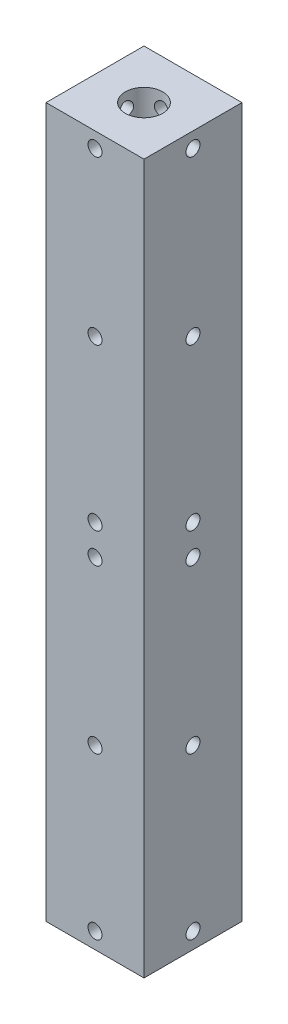
SolidWorks part; units mm, degrees
ref_plane "Front Plane" through (0, 0, 0) normal (0, 0, 1) x (1, 0, 0)
ref_plane "Top Plane" through (0, 0, 0) normal (0, 1, 0) x (1, 0, 0)
ref_plane "Right Plane" through (0, 0, 0) normal (1, 0, 0) x (0, 0, -1)
sketch "Sketch1" plane through (0, 0, 0) normal (0, 1, 0) x (1, 0, 0)
  line L1 (0, 0) -> (21, 0)
  line L2 (0, 0) -> (0, 21)
  line L3 (0, 21) -> (21, 21)
  line L4 (21, 0) -> (21, 21)
  line L5 (0, 0) -> (21, 21) construction
  line L6 (0, 21) -> (21, 0) construction
  point P4 (10.5, 10.5)
  dimension "D1" = 21
  dimension "D2" = 21
extrude "Boss-Extrude1" add sketch "Sketch1" along normal blind 152
sketch "Sketch2" plane through (0, 152, 0) normal (0, 1, 0) x (1, 0, 0)
  line L0 (0, 0) -> (21, 0) construction
  line L1 (0, 21) -> (0, 0) construction
  circle A0 centre (10.5, 10.5) radius 4
  dimension "D1" = 8
  dimension "D2" = 10.5
  dimension "D3" = 10.5
extrude "Cut-Extrude1" cut sketch "Sketch2" against normal blind 152
hole_wizard "Ø3.0mm Dowel Hole1" positions "Sketch3" profile "Sketch5" hole size "Ø3.0" standard "ANSI Metric"
sketch "Sketch3" plane through (0, 0, 0) normal (0, 0, 1) x (1, 0, 0)
  line L0 (0, 0) -> (21, 0) construction
  line L1 (0, 152) -> (0, 0) construction
  point P0 (10.5, 37.95)
  dimension "D1" = 37.95
  dimension "D2" = 10.5
sketch "Sketch5" plane through (10.5, 37.95, 0) normal (1, 0, 0) x (0, -1, 0)
  line L0 (0, 0) -> (0, 4.9013)
  line L1 (0, 4.9013) -> (1.5, 4)
  line L2 (1.5, 4) -> (1.5, 0)
  line L5 (1.5, 0) -> (0, 0)
  line L10 (0, 4.9013) -> (-1.5, 4) construction
  line L11 (0, -6.35) -> (0, 107.95) construction
  dimension "Hole Dia." = 3
  dimension "Hole Depth" = 4
  dimension "Drill Angle" = 118
pattern_linear "LPattern1" count 2 spacing 75.9 along (0, 1, 0) of "Ø3.0mm Dowel Hole1"
pattern_circular "CirPattern1" count 4 over 360 about axis through (10.5, 0, -10.5) along (0, 1, 0) of "LPattern1", "Ø3.0mm Dowel Hole1"
sketch "Sketch6" plane through (0, 0, 0) normal (0, 0, 1) x (1, 0, 0)
  line L0 (0, 152) -> (21, 152) construction
  line L1 (21, 152) -> (21, 0) construction
  circle A0 centre (10.5, 148.75) radius 1.5
  circle A1 centre (10.5, 79.35) radius 1.5
  dimension "D1" = 3
  dimension "D2" = 3.25
  dimension "D3" = 10.5
  dimension "D4" = 3
  dimension "D5" = 72.65
  dimension "D6" = 10.5
extrude "Cut-Extrude2" cut sketch "Sketch6" against normal up to next
pattern_linear "LPattern2" count 2 spacing 75.9 along (0, -1, 0) of "Cut-Extrude2"
pattern_circular "CirPattern2" count 4 over 360 about axis through (10.5, 0, -10.5) along (0, 1, 0) of "LPattern2", "Cut-Extrude2"
